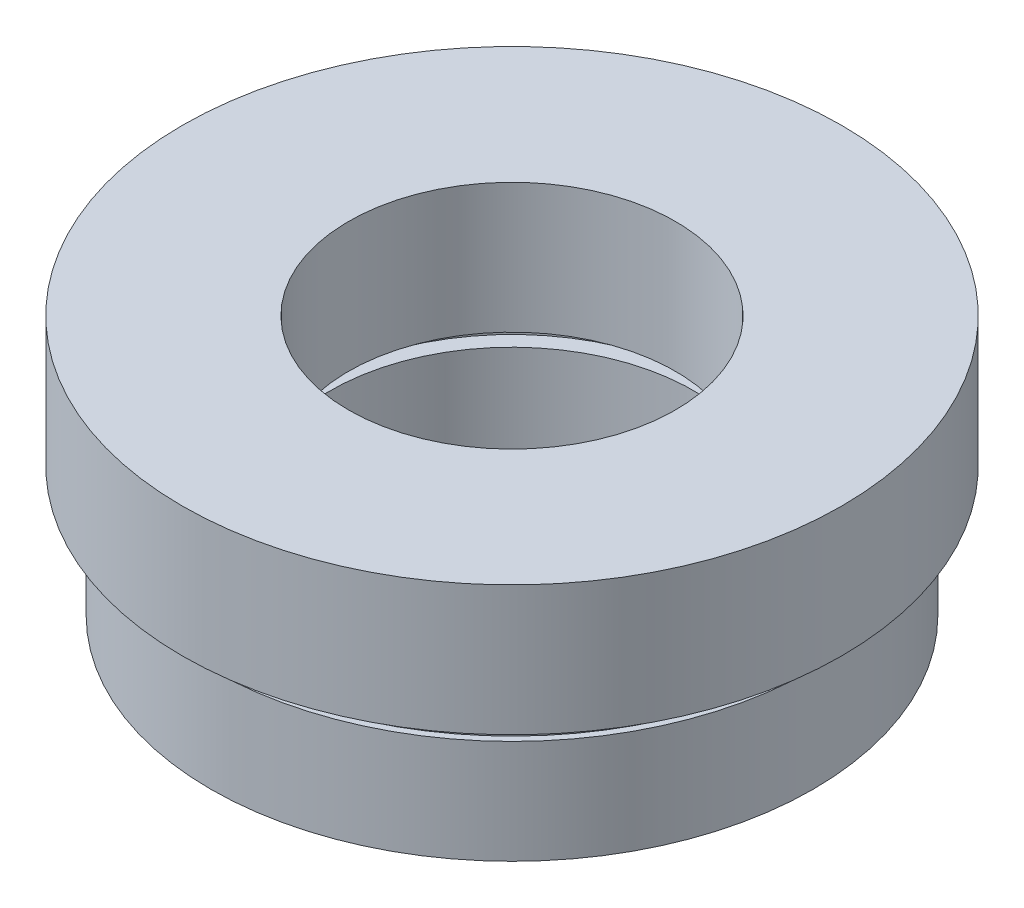
SolidWorks part; units mm, degrees
ref_plane "前视基准面" through (0, 0, 0) normal (0, 0, 1) x (1, 0, 0)
ref_plane "上视基准面" through (0, 0, 0) normal (0, 1, 0) x (1, 0, 0)
ref_plane "右视基准面" through (0, 0, 0) normal (1, 0, 0) x (0, 0, -1)
sketch "草图1" plane through (0, 0, 0) normal (0, 0, 1) x (1, 0, 0)
  line L0 (0, 13.7447) -> (0, -9.3128) construction
  line L1 (11.6, 0) -> (7, 0)
  line L2 (7, 0) -> (7, 4)
  line L3 (7, 4) -> (7.6, 4)
  line L4 (7.6, 4) -> (7.6, 5)
  line L5 (7.6, 5) -> (6.295, 5)
  line L6 (6.295, 5) -> (6.295, 10)
  line L7 (6.295, 10) -> (12.7, 10)
  line L8 (12.7, 10) -> (12.7, 5)
  line L9 (12.7, 5) -> (11.35, 5)
  line L10 (11.35, 5) -> (11.35, 4)
  line L11 (11.35, 4) -> (11.6, 4)
  line L12 (11.6, 4) -> (11.6, 0)
  dimension "D1" = 10
  dimension "D2" = 12.7
  dimension "D3" = 6.295
  dimension "D4" = 7
  dimension "D5" = 7.6
  dimension "D6" = 11.6
  dimension "D7" = 11.35
  dimension "D8" = 1
  dimension "D9" = 1
  dimension "D10" = 5
  dimension "D11" = 5
revolve "旋转1" add sketch "草图1" angle 360 about L0
cosmetic thread "装饰螺纹线1" parameters "D2"=13.59
cosmetic thread "装饰螺纹线2" parameters "D2"=15
cosmetic thread "装饰螺纹线3" parameters "D2"=22.2
